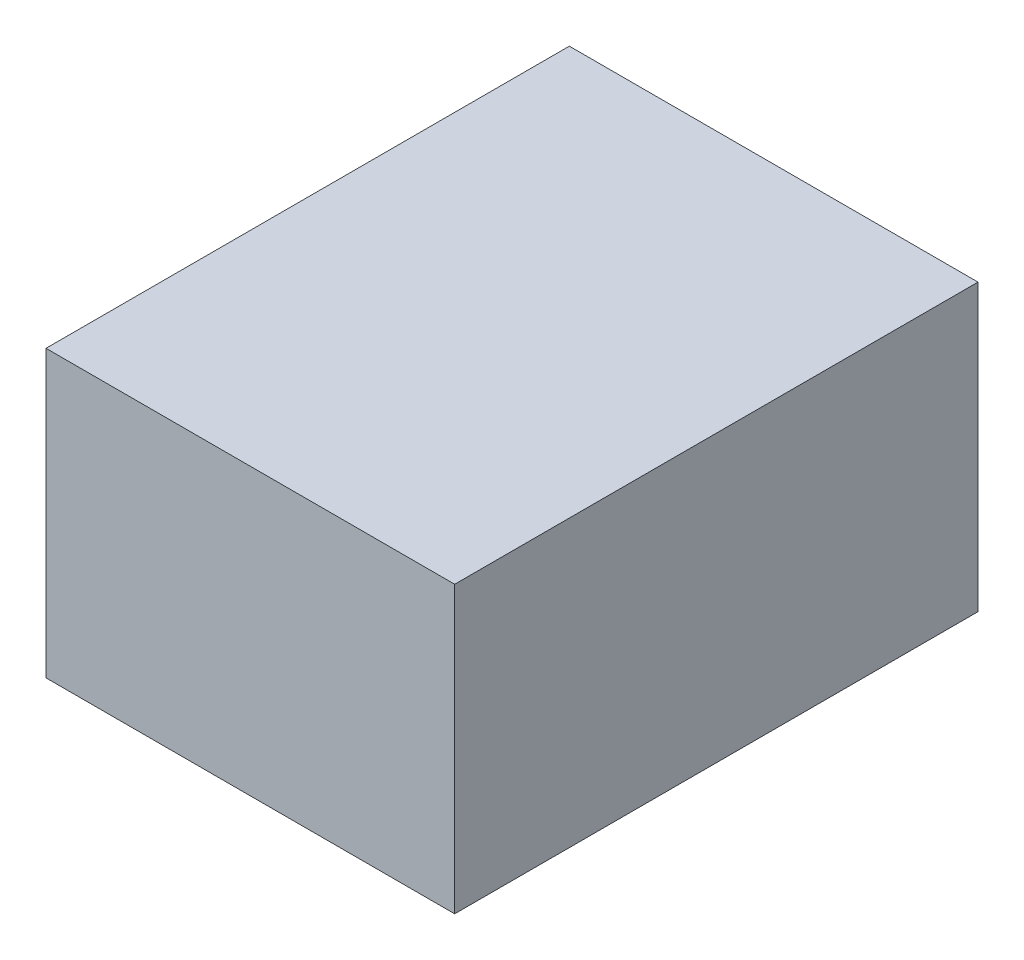
SolidWorks part; units mm, degrees
ref_plane "Front Plane" through (0, 0, 0) normal (0, 0, 1) x (1, 0, 0)
ref_plane "Top Plane" through (0, 0, 0) normal (0, 1, 0) x (1, 0, 0)
ref_plane "Right Plane" through (0, 0, 0) normal (1, 0, 0) x (0, 0, -1)
sketch "Sketch1" plane through (0, 0, 0) normal (0, 0, 1) x (1, 0, 0)
  line L1 (0, 0) -> (17.18, 0)
  line L2 (0, 0) -> (0, 12)
  line L3 (0, 12) -> (17.18, 12)
  line L4 (17.18, 0) -> (17.18, 12)
  dimension "D1" = 12
  dimension "D2" = 17.18
extrude "Boss-Extrude1" add sketch "Sketch1" along normal blind 22
